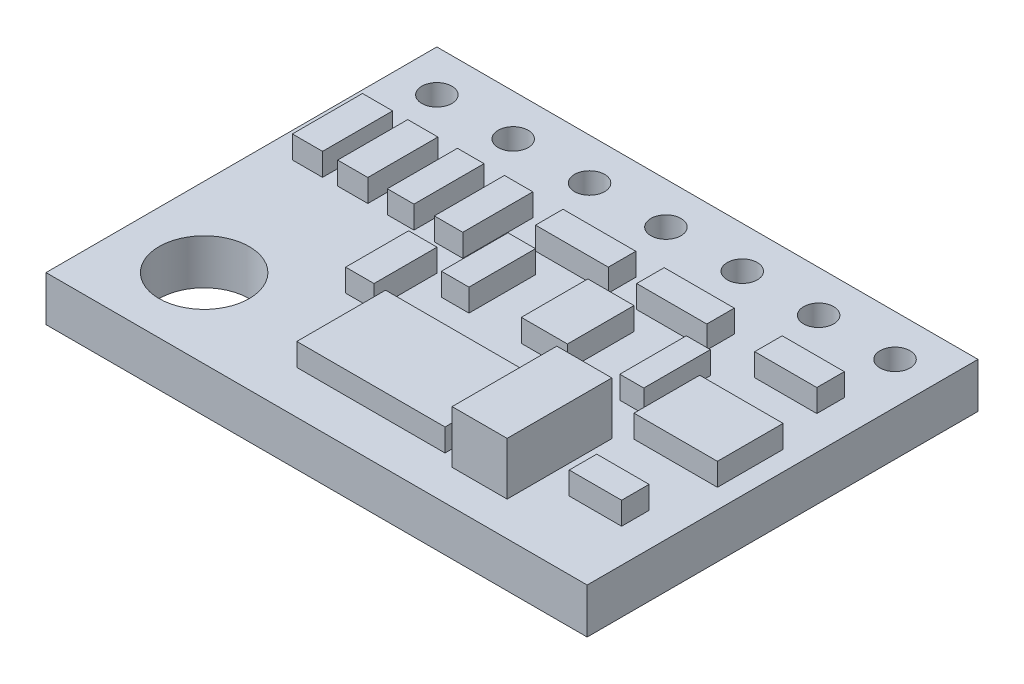
SolidWorks part; units mm, degrees
material "Brass"
ref_plane "Front Plane" through (0, 0, 0) normal (0, 0, 1) x (1, 0, 0)
ref_plane "Top Plane" through (0, 0, 0) normal (0, 1, 0) x (1, 0, 0)
ref_plane "Right Plane" through (0, 0, 0) normal (1, 0, 0) x (0, 0, -1)
sketch "Sketch1" plane through (0, 0, 0) normal (0, 1, 0) x (1, 0, 0)
  line L0 (1.38, -1.38) -> (3.92, -1.38) construction
  line L1 (0, 0) -> (18, 0)
  line L2 (0, 0) -> (0, -13)
  line L3 (0, -13) -> (18, -13)
  line L4 (18, 0) -> (18, -13)
  circle A0 centre (1.38, -1.38) radius 0.5
  circle A1 centre (3.92, -1.38) radius 0.5
  circle A2 centre (6.46, -1.38) radius 0.5
  circle A3 centre (9, -1.38) radius 0.5
  circle A4 centre (11.54, -1.38) radius 0.5
  circle A5 centre (14.08, -1.38) radius 0.5
  circle A6 centre (16.62, -1.38) radius 0.5
  circle A7 centre (2.63, -10.37) radius 1.5
  dimension "D3" = 7
  dimension "D5" = 1
  dimension "D8" = 3
  dimension "D1" = 18
  dimension "D2" = 13
  dimension "D4" = 2.54
  dimension "D6" = 1.38
  dimension "D7" = 1.38
  dimension "D9" = 2.63
  dimension "D10" = 2.63
extrude "Boss-Extrude1" add sketch "Sketch1" against normal blind 1.5
sketch "Sketch2" plane through (0, 0, 0) normal (0, 1, 0) x (1, 0, 0)
  line L1 (12.3647, -8.3742) -> (14.1946, -8.3742)
  line L2 (12.3647, -8.3742) -> (12.3647, -11.8569)
  line L3 (12.3647, -11.8569) -> (14.1946, -11.8569)
  line L4 (14.1946, -8.3742) -> (14.1946, -11.8569)
extrude "Boss-Extrude2" add sketch "Sketch2" along normal blind 1.75
sketch "Sketch3" plane through (0, 0, 0) normal (0, 1, 0) x (1, 0, 0)
  line L1 (6.9045, -8.6103) -> (11.8334, -8.6103)
  line L2 (6.9045, -8.6103) -> (6.9045, -11.5618)
  line L3 (6.9045, -11.5618) -> (11.8334, -11.5618)
  line L4 (11.8334, -8.6103) -> (11.8334, -11.5618)
  line L5 (0.8539, -3.3272) -> (1.8574, -3.3272)
  line L6 (0.8539, -3.3272) -> (0.8539, -5.6588)
  line L7 (0.8539, -5.6588) -> (1.8574, -5.6588)
  line L8 (1.8574, -3.3272) -> (1.8574, -5.6588)
  line L9 (2.3592, -3.3272) -> (3.3627, -3.3272)
  line L10 (2.3592, -3.3272) -> (2.3592, -5.6588)
  line L11 (2.3592, -5.6588) -> (3.3627, -5.6588)
  line L12 (3.3627, -3.3272) -> (3.3627, -5.6588)
  line L13 (4.012, -3.3272) -> (4.8975, -3.3272)
  line L14 (4.012, -3.3272) -> (4.012, -5.6588)
  line L15 (4.012, -5.6588) -> (4.8975, -5.6588)
  line L16 (4.8975, -3.3272) -> (4.8975, -5.6588)
  line L17 (5.5763, -3.3272) -> (6.5208, -3.3272)
  line L18 (5.5763, -3.3272) -> (5.5763, -5.6588)
  line L19 (5.5763, -5.6588) -> (6.5208, -5.6588)
  line L20 (6.5208, -3.3272) -> (6.5208, -5.6588)
  line L21 (5.5763, -6.5148) -> (6.5208, -6.5148)
  line L22 (5.5763, -6.5148) -> (5.5763, -8.6103)
  line L23 (5.5763, -8.6103) -> (6.5208, -8.6103)
  line L24 (6.5208, -6.5148) -> (6.5208, -8.6103)
  line L25 (7.2881, -4.921) -> (8.2031, -4.921)
  line L26 (7.2881, -4.921) -> (7.2881, -7.1346)
  line L27 (7.2881, -7.1346) -> (8.2031, -7.1346)
  line L28 (8.2031, -4.921) -> (8.2031, -7.1346)
  line L29 (7.5243, -3.3272) -> (9.9445, -3.3272)
  line L30 (7.5243, -3.3272) -> (7.5243, -4.2421)
  line L31 (7.5243, -4.2421) -> (9.9445, -4.2421)
  line L32 (9.9445, -3.3272) -> (9.9445, -4.2421)
  line L33 (10.8889, -3.3272) -> (13.2206, -3.3272)
  line L34 (10.8889, -3.3272) -> (10.8889, -4.2421)
  line L35 (10.8889, -4.2421) -> (13.2206, -4.2421)
  line L36 (13.2206, -3.3272) -> (13.2206, -4.2421)
  line L37 (14.8144, -3.3272) -> (16.8804, -3.3272)
  line L38 (14.8144, -3.3272) -> (14.8144, -4.2421)
  line L39 (14.8144, -4.2421) -> (16.8804, -4.2421)
  line L40 (16.8804, -3.3272) -> (16.8804, -4.2421)
  line L41 (13.2206, -4.921) -> (14.0175, -4.921)
  line L42 (13.2206, -4.921) -> (13.2206, -7.1346)
  line L43 (13.2206, -7.1346) -> (14.0175, -7.1346)
  line L44 (14.0175, -4.921) -> (14.0175, -7.1346)
  line L45 (14.5783, -5.8359) -> (17.3527, -5.8359)
  line L46 (14.5783, -5.8359) -> (14.5783, -8.02)
  line L47 (14.5783, -8.02) -> (17.3527, -8.02)
  line L48 (17.3527, -5.8359) -> (17.3527, -8.02)
  line L49 (15.1391, -9.8204) -> (16.8804, -9.8204)
  line L50 (15.1391, -9.8204) -> (15.1391, -10.7354)
  line L51 (15.1391, -10.7354) -> (16.8804, -10.7354)
  line L52 (16.8804, -9.8204) -> (16.8804, -10.7354)
  line L53 (9.9445, -4.921) -> (11.4792, -4.921)
  line L54 (9.9445, -4.921) -> (9.9445, -7.1346)
  line L55 (9.9445, -7.1346) -> (11.4792, -7.1346)
  line L56 (11.4792, -4.921) -> (11.4792, -7.1346)
extrude "Boss-Extrude3" add sketch "Sketch3" along normal blind 0.75
